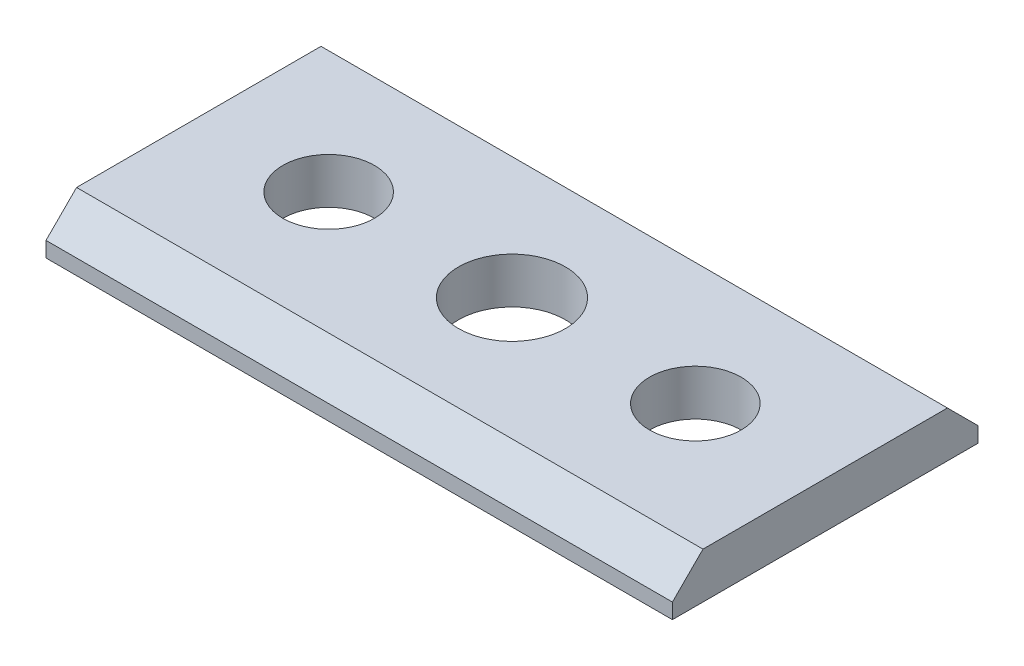
SolidWorks part; units mm, degrees
material "ABS"
ref_plane "Front Plane" through (0, 0, 0) normal (0, 0, 1) x (1, 0, 0)
ref_plane "Top Plane" through (0, 0, 0) normal (0, 1, 0) x (1, 0, 0)
ref_plane "Right Plane" through (0, 0, 0) normal (1, 0, 0) x (0, 0, -1)
sketch "Sketch1" plane through (0, 0, 0) normal (0, 1, 0) x (1, 0, 0)
  line L0 (0, 20) -> (0, 0)
  line L1 (0, 0) -> (41, 0)
  line L2 (41, 0) -> (41, 20)
  line L3 (41, 20) -> (0, 20)
  dimension "D1" = 41
  dimension "D2" = 20
extrude "Boss-Extrude1" add sketch "Sketch1" against normal blind 3
sketch "Sketch2" plane through (0, 0, 0) normal (0, 1, 0) x (1, 0, 0)
  line L6 (20.5, 20) -> (20.5, 0) construction
  line L7 (41, 20) -> (0, 20) construction
  line L8 (0, 0) -> (41, 0) construction
  line L9 (0, 10) -> (41, 10) construction
  line L10 (0, 20) -> (0, 0) construction
  line L11 (41, 0) -> (41, 20) construction
  line L13 (20.5, 5.1503) -> (24.7, 7.5751)
  line L14 (24.7, 7.5751) -> (24.7, 12.4249)
  line L15 (24.7, 12.4249) -> (20.5, 14.8497)
  line L16 (20.5, 14.8497) -> (16.3, 12.4249)
  line L17 (16.3, 12.4249) -> (16.3, 7.5751)
  line L18 (16.3, 7.5751) -> (20.5, 5.1503)
  circle A0 centre (20.5, 10) radius 4.2 construction
  dimension "D2" = 8.4
sketch "Sketch7" plane through (0, 0, 0) normal (0, 1, 0) x (1, 0, 0)
  line L0 (20.5, 20) -> (20.5, 0) construction
  line L1 (41, 20) -> (0, 20) construction
  line L2 (0, 0) -> (41, 0) construction
  line L3 (0, 10) -> (41, 10) construction
  line L4 (0, 20) -> (0, 0) construction
  line L5 (41, 0) -> (41, 20) construction
  circle A0 centre (8.5, 10) radius 3
  circle A1 centre (32.5, 10) radius 3
  circle A2 centre (20.5, 10) radius 3.5
  dimension "D1" = 6
  dimension "D2" = 12
  dimension "D3" = 7
extrude "holes" cut sketch "Sketch7" against normal through all
chamfer "Chamfer1" distance 2 angle 45 2 edges at (20.5, 0, -20) (20.5, 0, 0)
